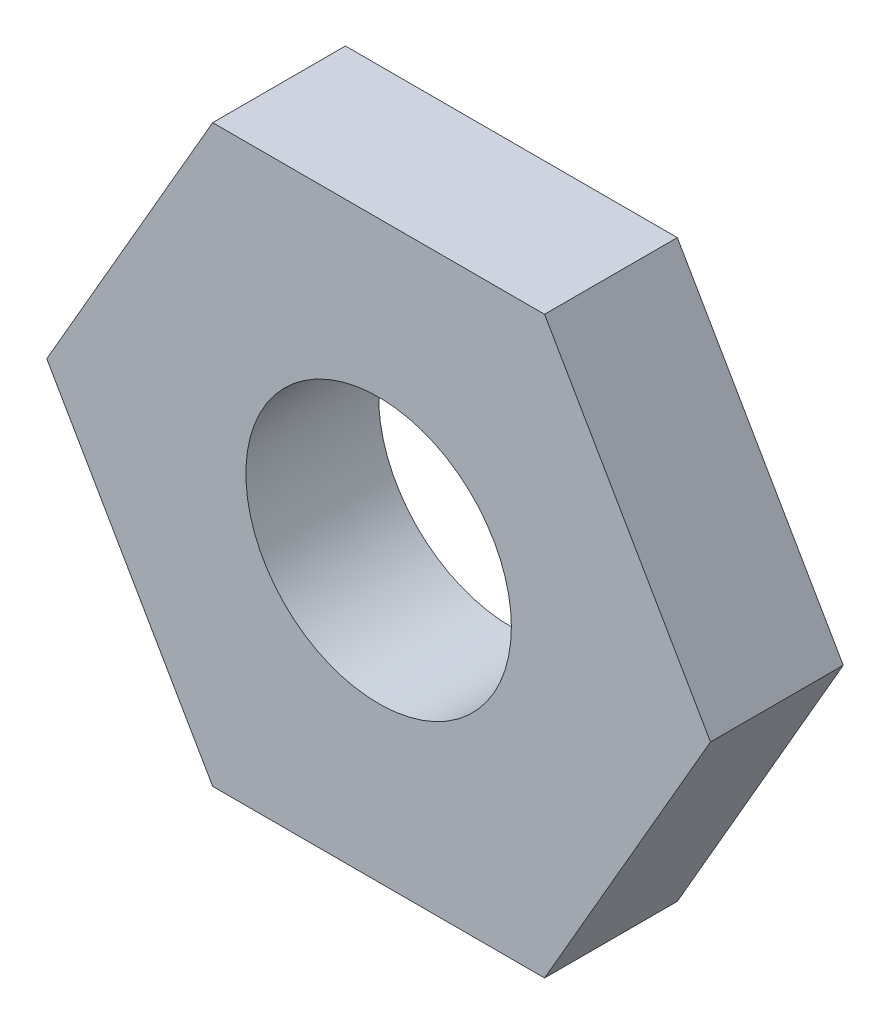
SolidWorks part; units mm, degrees
ref_plane "Plan de face" through (0, 0, 0) normal (0, 0, 1) x (1, 0, 0)
ref_plane "Plan de dessus" through (0, 0, 0) normal (0, 1, 0) x (1, 0, 0)
ref_plane "Plan de droite" through (0, 0, 0) normal (1, 0, 0) x (0, 0, -1)
sketch "Esquisse1" plane through (0, 0, 0) normal (0, 0, 1) x (1, 0, 0)
  line L0 (-5, 0) -> (-2.5, 4.3301)
  line L1 (-2.5, 4.3301) -> (2.5, 4.3301)
  line L2 (2.5, 4.3301) -> (5, 0)
  line L3 (5, 0) -> (2.5, -4.3301)
  line L4 (2.5, -4.3301) -> (-2.5, -4.3301)
  line L5 (-2.5, -4.3301) -> (-5, 0)
  line L6 (-5, 0) -> (0, 0) construction
  line L7 (0, 0) -> (5, 0) construction
  circle A0 centre (0, 0) radius 2
  dimension "D3" = 4
  dimension "D1" = 120
  dimension "D2" = 120
  dimension "D4" = 5
extrude "Boss.-Extru.1" add sketch "Esquisse1" along normal blind 2
